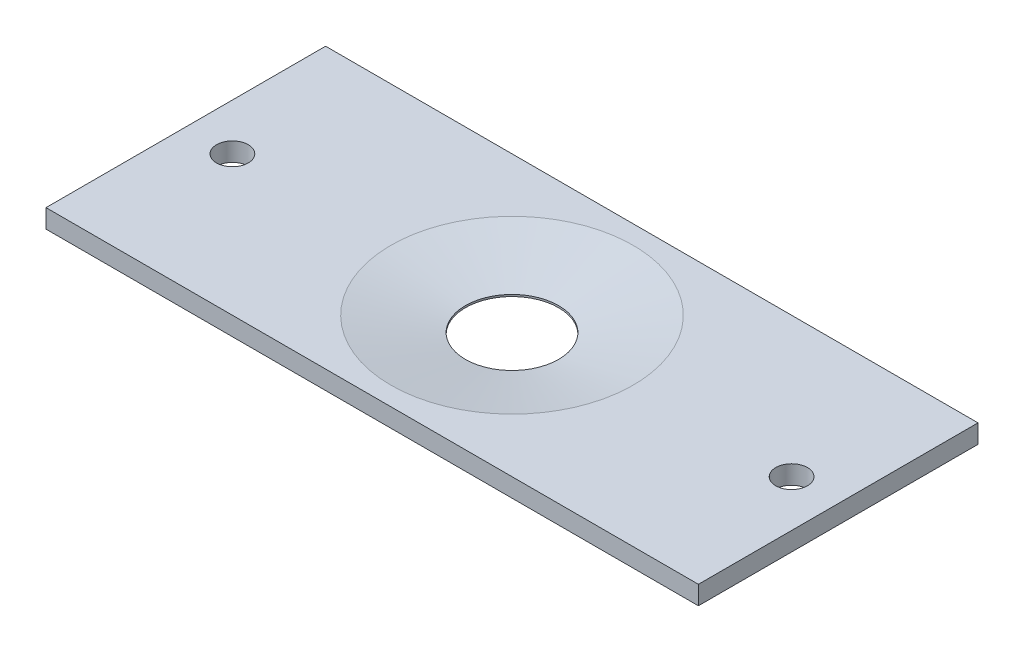
SolidWorks part; units mm, degrees
ref_plane "Front Plane" through (0, 0, 0) normal (0, 0, 1) x (1, 0, 0)
ref_plane "Top Plane" through (0, 0, 0) normal (0, 1, 0) x (1, 0, 0)
ref_plane "Right Plane" through (0, 0, 0) normal (1, 0, 0) x (0, 0, -1)
sketch "Sketch1" plane through (0, 0, 0) normal (0, 1, 0) x (1, 0, 0)
  line L1 (-35, 15) -> (35, 15)
  line L2 (-35, 15) -> (-35, -15)
  line L3 (-35, -15) -> (35, -15)
  line L4 (35, 15) -> (35, -15)
  circle A0 centre (0, 0) radius 5
  dimension "D5" = 10
  dimension "D1" = 35
  dimension "D2" = 35
  dimension "D3" = 15
  dimension "D4" = 15
extrude "Extrude1" add sketch "Sketch1" along normal blind 2
chamfer "Chamfer1" distance 8 distance2 1.6 1 edges at (0, 2, 5)
sketch "Sketch3" plane through (0, 0, 0) normal (0, -1, 0) x (1, 0, 0)
  circle A0 centre (0, 0) radius 5.5
extrude "Cut-Extrude1" cut sketch "Sketch3" against normal blind 0.2
hole_wizard "M3 Clearance Hole1" positions "Sketch6" profile "Sketch5" hole size "M3" standard "ISO" end condition through all
sketch "Sketch6" plane through (0, 2, 0) normal (0, 1, 0) x (-1, 0, 0)
  line L0 (-35, 15) -> (-35, -15) construction
  line L1 (35, -15) -> (35, 15) construction
  line L3 (-35, -15) -> (35, -15) construction
  point P0 (-30, 0)
  point P5 (30, 0)
  dimension "D1" = 5
  dimension "D2" = 5
  dimension "D3" = 15
sketch "Sketch5" plane through (30, 2, 0) normal (1, 0, 0) x (0, 0, 1)
  line L0 (0, 0) -> (0, 2)
  line L1 (0, 2) -> (1.7, 2)
  line L2 (1.7, 2) -> (1.7, 0)
  line L5 (1.7, 0) -> (0, 0)
  line L11 (0, -6.35) -> (0, 107.95) construction
  dimension "Thru Hole Dia." = 3.4
  dimension "Thru Hole Depth" = 2
equation "\"D2@Sketch1\" = \"D1@Sketch1\""
equation "\"D4@Sketch1\" = \"D3@Sketch1\""
equation "\"D2@Sketch6\" = \"D1@Sketch6\""
